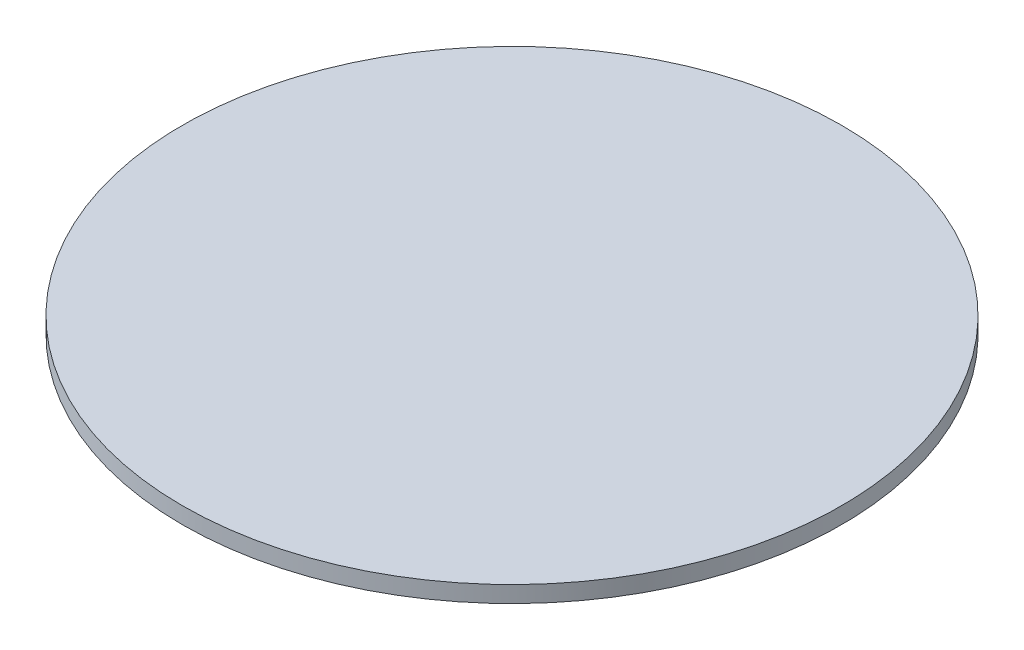
SolidWorks part; units mm, degrees
material "Acrylic (Medium-high impact)"
ref_plane "Front Plane" through (0, 0, 0) normal (0, 0, 1) x (1, 0, 0)
ref_plane "Top Plane" through (0, 0, 0) normal (0, 1, 0) x (1, 0, 0)
ref_plane "Right Plane" through (0, 0, 0) normal (1, 0, 0) x (0, 0, -1)
sketch "Sketch1" plane through (0, 0, 0) normal (0, 1, 0) x (1, 0, 0)
  circle A0 centre (0, 0) radius 127
extrude "Boss-Extrude1" add sketch "Sketch1" along normal blind 6.35
